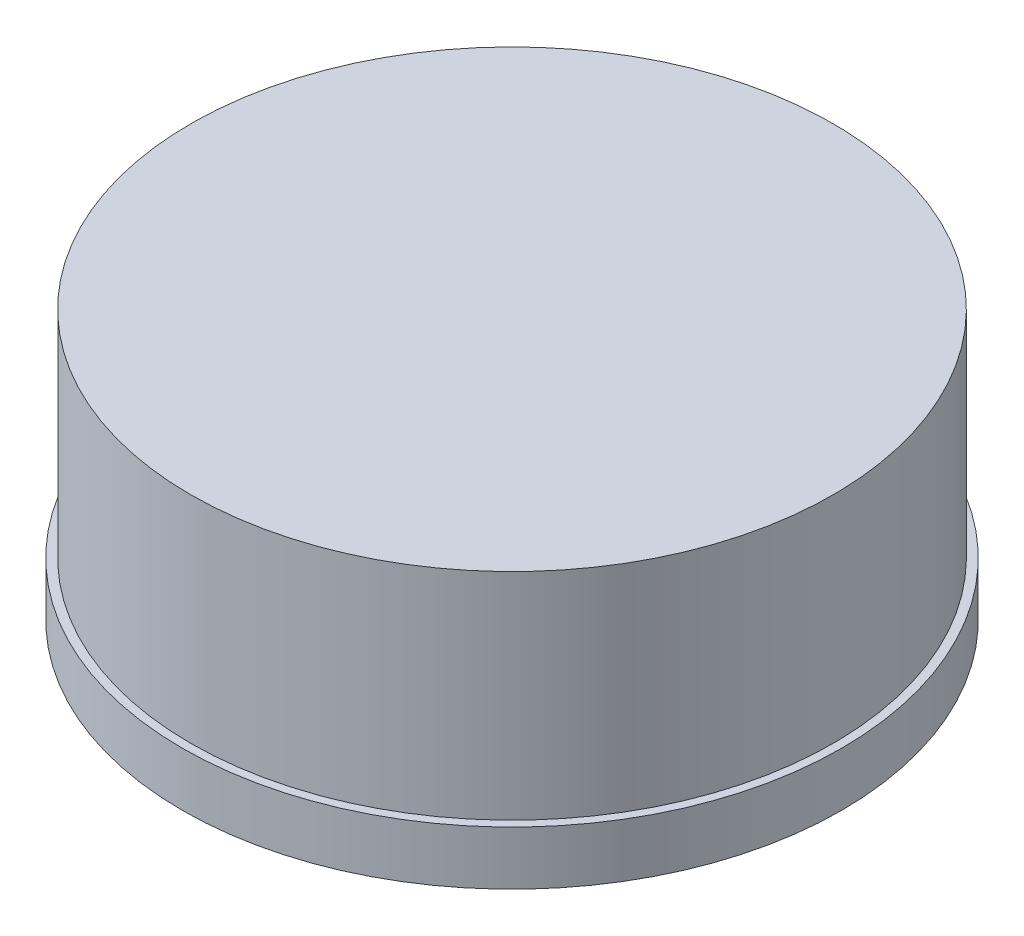
SolidWorks part; units mm, degrees
ref_plane "Front Plane" through (0, 0, 0) normal (0, 0, 1) x (1, 0, 0)
ref_plane "Top Plane" through (0, 0, 0) normal (0, 1, 0) x (1, 0, 0)
ref_plane "Right Plane" through (0, 0, 0) normal (1, 0, 0) x (0, 0, -1)
sketch "Sketch1" plane through (0, 0, 0) normal (0, 1, 0) x (1, 0, 0)
  circle A0 centre (0, 0) radius 4.9
extrude "Boss-Extrude1" add sketch "Sketch1" along normal blind 0.8
sketch "Sketch2" plane through (0, 0.8, 0) normal (0, 1, 0) x (1, 0, 0)
  circle A0 centre (0, 0) radius 4.775
extrude "Boss-Extrude2" add sketch "Sketch2" along normal blind 3.2
sketch "Sketch3" plane through (0, 0, 0) normal (0, -1, 0) x (-1, 0, 0)
  circle A0 centre (0, 0) radius 4.05
extrude "Cut-Extrude1" cut sketch "Sketch3" against normal blind 3.2
